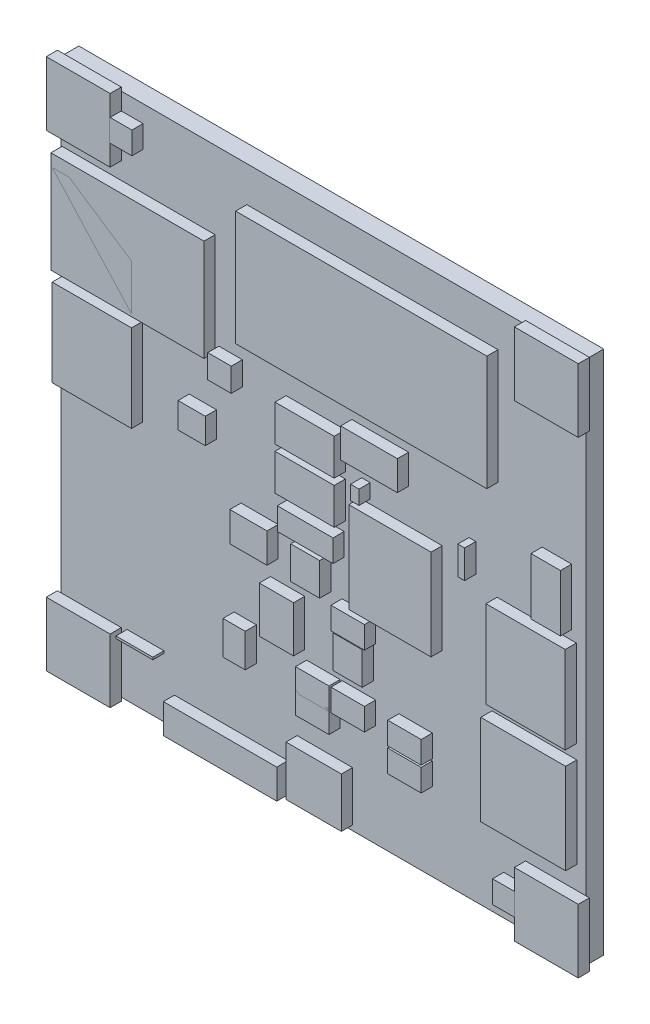
SolidWorks part; units mm, degrees
ref_plane "Front Plane" through (0, 0, 0) normal (0, 0, 1) x (1, 0, 0)
ref_plane "Top Plane" through (0, 0, 0) normal (0, 1, 0) x (1, 0, 0)
ref_plane "Right Plane" through (0, 0, 0) normal (1, 0, 0) x (0, 0, -1)
sketch "Sketch1" plane through (0, 0, 0) normal (0, 0, 1) x (1, 0, 0)
  line L0 (0, 46.99) -> (46.99, 46.99)
  line L1 (46.99, 46.99) -> (46.99, 0)
  line L2 (46.99, 0) -> (0, 0)
  line L3 (0, 0) -> (0, 46.99)
extrude "BOARD" add sketch "Sketch1" along normal blind 1.6 separate body
ref_plane "Plane1" through (0, 0, 1.6) normal (0, 0, 1) x (1, 0, 0)
sketch "Sketch2" plane through (0, 0, 1.6) normal (0, 0, 1) x (1, 0, 0)
  line L0 (16.1165, 20.4135) -> (19.4435, 20.4135)
  line L1 (19.4435, 20.4135) -> (19.4435, 17.75)
  line L2 (19.4435, 17.75) -> (16.1165, 17.75)
  line L3 (16.1165, 17.75) -> (16.1165, 20.4135)
extrude "1210-1" add sketch "Sketch2" along normal blind 1 separate body
sketch "Sketch3" plane through (0, 0, 1.6) normal (0, 0, 1) x (1, 0, 0)
  line L0 (25.3584, 20.8356) -> (20.3616, 20.8356)
  line L1 (20.3616, 20.8356) -> (20.3616, 22.827)
  line L2 (20.3616, 22.827) -> (25.3584, 22.827)
  line L3 (25.3584, 22.827) -> (25.3584, 20.8356)
extrude "1206-1" add sketch "Sketch3" along normal blind 1 separate body
sketch "Sketch4" plane through (0, 0, 1.6) normal (0, 0, 1) x (1, 0, 0)
  line L0 (20.1584, 30.76) -> (25.46, 30.76)
  line L1 (25.46, 30.76) -> (25.46, 27.5084)
  line L2 (25.46, 27.5084) -> (20.1584, 27.5084)
  line L3 (20.1584, 27.5084) -> (20.1584, 30.76)
extrude "EIA3528-1" add sketch "Sketch4" along normal blind 1 separate body
sketch "Sketch5" plane through (0, 0, 1.6) normal (0, 0, 1) x (1, 0, 0)
  line L0 (20.1584, 26.95) -> (25.46, 26.95)
  line L1 (25.46, 26.95) -> (25.46, 23.6984)
  line L2 (25.46, 23.6984) -> (20.1584, 23.6984)
  line L3 (20.1584, 23.6984) -> (20.1584, 26.95)
extrude "EIA3528-2" add sketch "Sketch5" along normal blind 1 separate body
sketch "Sketch6" plane through (0, 0, 1.6) normal (0, 0, 1) x (1, 0, 0)
  line L0 (25.1716, 17.5184) -> (28.1684, 17.5184)
  line L1 (28.1684, 17.5184) -> (28.1684, 15.527)
  line L2 (28.1684, 15.527) -> (25.1716, 15.527)
  line L3 (25.1716, 15.527) -> (25.1716, 17.5184)
extrude "0603-CAP-1" add sketch "Sketch6" along normal blind 1 separate body
sketch "Sketch7" plane through (0, 0, 1.6) normal (0, 0, 1) x (1, 0, 0)
  line L0 (15.5016, 8.6616) -> (15.5016, 11.6584)
  line L1 (15.5016, 11.6584) -> (17.493, 11.6584)
  line L2 (17.493, 11.6584) -> (17.493, 8.6616)
  line L3 (17.493, 8.6616) -> (15.5016, 8.6616)
extrude "0603-CAP-2" add sketch "Sketch7" along normal blind 1 separate body
sketch "Sketch8" plane through (0, 0, 1.6) normal (0, 0, 1) x (1, 0, 0)
  line L0 (24.1554, 20.4724) -> (24.1554, 17.5514)
  line L1 (24.1554, 17.5514) -> (21.5646, 17.5514)
  line L2 (21.5646, 17.5514) -> (21.5646, 20.4724)
  line L3 (21.5646, 20.4724) -> (24.1554, 20.4724)
extrude "SOT23-1" add sketch "Sketch8" along normal blind 1 separate body
sketch "Sketch9" plane through (0, 0, 1.6) normal (0, 0, 1) x (1, 0, 0)
  line L0 (25.3746, 12.5476) -> (25.3746, 15.4686)
  line L1 (25.3746, 15.4686) -> (27.9654, 15.4686)
  line L2 (27.9654, 15.4686) -> (27.9654, 12.5476)
  line L3 (27.9654, 12.5476) -> (25.3746, 12.5476)
extrude "SOT23-2" add sketch "Sketch9" along normal blind 1 separate body
sketch "Sketch10" plane through (0, 0, 1.6) normal (0, 0, 1) x (1, 0, 0)
  line L0 (7.35, 43.45) -> (5.35, 43.45)
  line L1 (5.35, 43.45) -> (5.35, 45.45)
  line L2 (5.35, 45.45) -> (7.35, 45.45)
  line L3 (7.35, 45.45) -> (7.35, 43.45)
extrude "FIDUCIAL-1X2-1" add sketch "Sketch10" along normal blind 1 separate body
sketch "Sketch11" plane through (0, 0, 1.6) normal (0, 0, 1) x (1, 0, 0)
  line L0 (41.64, 1.54) -> (39.64, 1.54)
  line L1 (39.64, 1.54) -> (39.64, 3.54)
  line L2 (39.64, 3.54) -> (41.64, 3.54)
  line L3 (41.64, 3.54) -> (41.64, 1.54)
extrude "FIDUCIAL-1X2-2" add sketch "Sketch11" along normal blind 1 separate body
sketch "POWER_JACK_SMD-1 [0]" plane through (0, 0, 1.6) normal (0, 0, 1) x (1, 0, 0)
  line L0 (-0.0216, 18.5716) -> (14.88, 18.5716)
  line L1 (14.88, 18.5716) -> (14.88, 9.3684)
  line L2 (14.88, 9.3684) -> (-0.0216, 9.3684)
  line L3 (-0.0216, 9.3684) -> (-0.0216, 18.5716)
sketch "Sketch14" plane through (0, 0, 1.6) normal (0, 0, 1) x (1, 0, 0)
  line L0 (13.8016, 40.06) -> (13.8016, 30.9584)
  line L1 (13.8016, 30.9584) -> (0.1, 30.9584)
  line L2 (0.1, 30.9584) -> (0.1, 40.06)
  line L3 (0.1, 40.06) -> (13.8016, 40.06)
extrude "POWER_JACK_PTH-1" add sketch "Sketch14" along normal blind 1 separate body
sketch "Sketch15" plane through (0, 0, 1.6) normal (0, 0, 1) x (1, 0, 0)
  line L0 (46.18, 15.5316) -> (46.18, 7.43)
  line L1 (46.18, 7.43) -> (38.5784, 7.43)
  line L2 (38.5784, 7.43) -> (38.5784, 15.5316)
  line L3 (38.5784, 15.5316) -> (46.18, 15.5316)
extrude "JST-2-SMD-1" add sketch "Sketch15" along normal blind 1 separate body
sketch "Sketch16" plane through (0, 0, 1.6) normal (0, 0, 1) x (1, 0, 0)
  line L0 (20.32, -0.1016) -> (10.16, -0.1016)
  line L1 (10.16, -0.1016) -> (10.16, 2.54)
  line L2 (10.16, 2.54) -> (20.32, 2.54)
  line L3 (20.32, 2.54) -> (20.32, -0.1016)
extrude "1X04-1" add sketch "Sketch16" along normal blind 1 separate body
sketch "Sketch17" plane through (0, 0, 1.6) normal (0, 0, 1) x (1, 0, 0)
  line L0 (43.0784, 25.4) -> (43.0784, 30.48)
  line L1 (43.0784, 30.48) -> (45.72, 30.48)
  line L2 (45.72, 30.48) -> (45.72, 25.4)
  line L3 (45.72, 25.4) -> (43.0784, 25.4)
extrude "1X02-1" add sketch "Sketch17" along normal blind 1 separate body
sketch "Sketch18" plane through (0, 0, 1.6) normal (0, 0, 1) x (1, 0, 0)
  line L0 (39.0434, 16.773) -> (39.0434, 24.573)
  line L1 (39.0434, 24.573) -> (46.145, 24.573)
  line L2 (46.145, 24.573) -> (46.145, 16.773)
  line L3 (46.145, 16.773) -> (39.0434, 16.773)
extrude "SCREWTERMINAL-3_5MM-2-1" add sketch "Sketch18" along normal blind 1 separate body
sketch "Sketch19" plane through (0, 0, 1.6) normal (0, 0, 1) x (1, 0, 0)
  line L0 (7.3116, 38.98) -> (7.3116, 31.18)
  line L1 (7.3116, 31.18) -> (0.21, 31.18)
  line L2 (0.21, 31.18) -> (0.21, 38.98)
  line L3 (0.21, 38.98) -> (7.3116, 38.98)
extrude "SCREWTERMINAL-3_5MM-2-2" add sketch "Sketch19" along normal blind 1 separate body
sketch "Sketch20" plane through (0, 0, 1.6) normal (0, 0, 1) x (1, 0, 0)
  line L0 (7.3116, 30.09) -> (7.3116, 22.29)
  line L1 (7.3116, 22.29) -> (0.21, 22.29)
  line L2 (0.21, 22.29) -> (0.21, 30.09)
  line L3 (0.21, 30.09) -> (7.3116, 30.09)
extrude "SCREWTERMINAL-3_5MM-2-3" add sketch "Sketch20" along normal blind 1 separate body
sketch "Sketch21" plane through (0, 0, 1.6) normal (0, 0, 1) x (1, 0, 0)
  line L0 (11.4808, 26.543) -> (13.9192, 26.543)
  line L1 (13.9192, 26.543) -> (13.9192, 24.257)
  line L2 (13.9192, 24.257) -> (11.4808, 24.257)
  line L3 (11.4808, 24.257) -> (11.4808, 26.543)
extrude "SJ_2S-1" add sketch "Sketch21" along normal blind 1 separate body
sketch "Sketch22" plane through (0, 0, 1.6) normal (0, 0, 1) x (1, 0, 0)
  line L0 (16.24, 31.5865) -> (16.24, 29.475)
  line L1 (16.24, 29.475) -> (14.1384, 29.475)
  line L2 (14.1384, 29.475) -> (14.1384, 31.5865)
  line L3 (14.1384, 31.5865) -> (16.24, 31.5865)
extrude "SJ_2S-NO-1" add sketch "Sketch22" along normal blind 1 separate body
sketch "Sketch23" plane through (0, 0, 1.6) normal (0, 0, 1) x (1, 0, 0)
  line L0 (36.5252, 27.94) -> (37.1348, 27.94)
  line L1 (37.1348, 27.94) -> (37.1348, 25.4)
  line L2 (37.1348, 25.4) -> (36.5252, 25.4)
  line L3 (36.5252, 25.4) -> (36.5252, 27.94)
extrude "PTH-JUMPER-NC_BOTTOM_NO_SILK-1" add sketch "Sketch23" along normal blind 1 separate body
sketch "Sketch24" plane through (0, 0, 1.6) normal (0, 0, 1) x (1, 0, 0)
  line L0 (26.035, 31.8516) -> (31.115, 31.8516)
  line L1 (31.115, 31.8516) -> (31.115, 29.21)
  line L2 (31.115, 29.21) -> (26.035, 29.21)
  line L3 (26.035, 29.21) -> (26.035, 31.8516)
extrude "1X02-2" add sketch "Sketch24" along normal blind 1 separate body
sketch "Sketch25" plane through (0, 0, 1.6) normal (0, 0, 1) x (1, 0, 0)
  line L0 (26.7665, 17.9865) -> (26.7665, 26.1135)
  line L1 (26.7665, 26.1135) -> (34.13, 26.1135)
  line L2 (34.13, 26.1135) -> (34.13, 17.9865)
  line L3 (34.13, 17.9865) -> (26.7665, 17.9865)
extrude "CR75-1" add sketch "Sketch25" along normal blind 1 separate body
sketch "Sketch26" plane through (0, 0, 1.6) normal (0, 0, 1) x (1, 0, 0)
  line L0 (16.637, 43.808) -> (39.127, 43.808)
  line L1 (39.127, 43.808) -> (39.127, 33.528)
  line L2 (39.127, 33.528) -> (16.637, 33.528)
  line L3 (16.637, 33.528) -> (16.637, 43.808)
extrude "SFE_LOGO_NAME_FLAME__2-1" add sketch "Sketch26" along normal blind 1 separate body
sketch "Sketch27" plane through (0, 0, 1.6) normal (0, 0, 1) x (1, 0, 0)
  line L0 (21.1406, 4.8944) -> (26.1034, 4.8944)
  line L1 (26.1034, 4.8944) -> (26.1034, 0.443)
  line L2 (26.1034, 0.443) -> (21.1406, 0.443)
  line L3 (21.1406, 0.443) -> (21.1406, 4.8944)
extrude "OSHW-LOGO-M-1" add sketch "Sketch27" along normal blind 1 separate body
sketch "Sketch28" plane through (0, 0, 0) normal (0, 0, 1) x (1, 0, 0)
  line L0 (4.0288, 9.1088) -> (1.0512, 9.1088)
  line L1 (1.0512, 9.1088) -> (1.0512, 6.438)
  line L2 (1.0512, 6.438) -> (4.0288, 6.438)
  line L3 (4.0288, 6.438) -> (4.0288, 9.1088)
extrude "OSHW-LOGO-S-1" add sketch "Sketch28" against normal blind 1 separate body
sketch "Sketch29" plane through (0, 0, 0) normal (0, 0, 1) x (1, 0, 0)
  line L0 (40.64, 30.66) -> (7.39, 30.66)
  line L1 (7.39, 30.66) -> (7.39, 15.24)
  line L2 (7.39, 15.24) -> (40.64, 15.24)
  line L3 (40.64, 15.24) -> (40.64, 30.66)
sketch "Sketch30" plane through (0, 0, 1.6) normal (0, 0, 1) x (1, 0, 0)
  line L0 (27.6812, 26.5018) -> (26.9288, 26.5018)
  line L1 (26.9288, 26.5018) -> (26.9288, 27.778)
  line L2 (26.9288, 27.778) -> (27.6812, 27.778)
  line L3 (27.6812, 27.778) -> (27.6812, 26.5018)
extrude "0805-1" add sketch "Sketch30" along normal blind 1 separate body
sketch "Sketch31" plane through (0, 0, 1.6) normal (0, 0, 1) x (1, 0, 0)
  line L0 (25.1716, 11.1684) -> (28.1684, 11.1684)
  line L1 (28.1684, 11.1684) -> (28.1684, 9.177)
  line L2 (28.1684, 9.177) -> (25.1716, 9.177)
  line L3 (25.1716, 9.177) -> (25.1716, 11.1684)
extrude "0603-RES-1" add sketch "Sketch31" along normal blind 1 separate body
sketch "Sketch32" plane through (0, 0, 1.6) normal (0, 0, 1) x (1, 0, 0)
  line L0 (21.9966, 9.3904) -> (24.9934, 9.3904)
  line L1 (24.9934, 9.3904) -> (24.9934, 7.399)
  line L2 (24.9934, 7.399) -> (21.9966, 7.399)
  line L3 (21.9966, 7.399) -> (21.9966, 9.3904)
extrude "0603-RES-2" add sketch "Sketch32" along normal blind 1 separate body
sketch "Sketch33" plane through (0, 0, 1.6) normal (0, 0, 1) x (1, 0, 0)
  line L0 (21.9966, 11.1684) -> (24.9934, 11.1684)
  line L1 (24.9934, 11.1684) -> (24.9934, 9.177)
  line L2 (24.9934, 9.177) -> (21.9966, 9.177)
  line L3 (21.9966, 9.177) -> (21.9966, 11.1684)
extrude "0603-RES-3" add sketch "Sketch33" along normal blind 1 separate body
sketch "Sketch34" plane through (0, 0, 1.6) normal (0, 0, 1) x (1, 0, 0)
  line L0 (33.2484, 9.1516) -> (30.2516, 9.1516)
  line L1 (30.2516, 9.1516) -> (30.2516, 11.143)
  line L2 (30.2516, 11.143) -> (33.2484, 11.143)
  line L3 (33.2484, 11.143) -> (33.2484, 9.1516)
extrude "0603-RES-4" add sketch "Sketch34" along normal blind 1 separate body
sketch "Sketch35" plane through (0, 0, 1.6) normal (0, 0, 1) x (1, 0, 0)
  line L0 (33.2484, 6.9926) -> (30.2516, 6.9926)
  line L1 (30.2516, 6.9926) -> (30.2516, 8.984)
  line L2 (30.2516, 8.984) -> (33.2484, 8.984)
  line L3 (33.2484, 8.984) -> (33.2484, 6.9926)
extrude "0603-RES-5" add sketch "Sketch35" along normal blind 1 separate body
sketch "Sketch36" plane through (0, 0, 1.6) normal (0, 0, 1) x (1, 0, 0)
  line L0 (5.9184, 5.5116) -> (9.22, 5.5116)
  line L1 (9.22, 5.5116) -> (9.22, 5.3084)
  line L2 (9.22, 5.3084) -> (5.9184, 5.3084)
  line L3 (5.9184, 5.3084) -> (5.9184, 5.5116)
extrude "TRIMPOT-3MM-1" add sketch "Sketch36" along normal blind 1 separate body
sketch "Sketch37" plane through (0, 0, 1.6) normal (0, 0, 1) x (1, 0, 0)
  line L0 (-0.3175, 5.3975) -> (5.3975, 5.3975)
  line L1 (5.3975, 5.3975) -> (5.3975, -0.3175)
  line L2 (5.3975, -0.3175) -> (-0.3175, -0.3175)
  line L3 (-0.3175, -0.3175) -> (-0.3175, 5.3975)
extrude "STAND-OFF-1" add sketch "Sketch37" along normal blind 1 separate body
sketch "Sketch38" plane through (0, 0, 1.6) normal (0, 0, 1) x (1, 0, 0)
  line L0 (-0.3175, 47.3075) -> (5.3975, 47.3075)
  line L1 (5.3975, 47.3075) -> (5.3975, 41.5925)
  line L2 (5.3975, 41.5925) -> (-0.3175, 41.5925)
  line L3 (-0.3175, 41.5925) -> (-0.3175, 47.3075)
extrude "STAND-OFF-2" add sketch "Sketch38" along normal blind 1 separate body
sketch "Sketch39" plane through (0, 0, 1.6) normal (0, 0, 1) x (1, 0, 0)
  line L0 (41.5925, 47.3075) -> (47.3075, 47.3075)
  line L1 (47.3075, 47.3075) -> (47.3075, 41.5925)
  line L2 (47.3075, 41.5925) -> (41.5925, 41.5925)
  line L3 (41.5925, 41.5925) -> (41.5925, 47.3075)
extrude "STAND-OFF-3" add sketch "Sketch39" along normal blind 1 separate body
sketch "Sketch40" plane through (0, 0, 1.6) normal (0, 0, 1) x (1, 0, 0)
  line L0 (41.5925, 5.3975) -> (47.3075, 5.3975)
  line L1 (47.3075, 5.3975) -> (47.3075, -0.3175)
  line L2 (47.3075, -0.3175) -> (41.5925, -0.3175)
  line L3 (41.5925, -0.3175) -> (41.5925, 5.3975)
extrude "STAND-OFF-4" add sketch "Sketch40" along normal blind 1 separate body
sketch "Sketch41" plane through (0, 0, 1.6) normal (0, 0, 1) x (1, 0, 0)
  line L0 (18.7565, 16.0335) -> (21.82, 16.0335)
  line L1 (21.82, 16.0335) -> (21.82, 11.9065)
  line L2 (21.82, 11.9065) -> (18.7565, 11.9065)
  line L3 (18.7565, 11.9065) -> (18.7565, 16.0335)
extrude "MSOP-12_GND-1" add sketch "Sketch41" along normal blind 1 separate body
